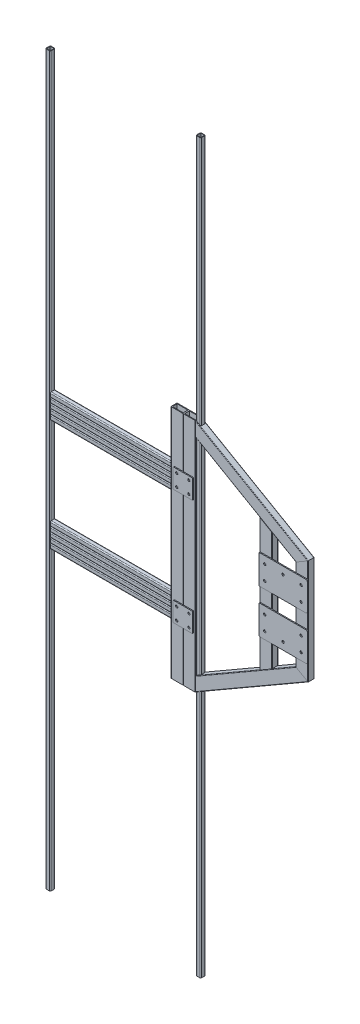
SolidWorks part; units mm, degrees
ref_plane "Front Plane" through (0, 0, 0) normal (0, 0, 1) x (1, 0, 0)
ref_plane "Top Plane" through (0, 0, 0) normal (0, 1, 0) x (1, 0, 0)
ref_plane "Right Plane" through (0, 0, 0) normal (1, 0, 0) x (0, 0, -1)
sketch "Sketch1" plane through (0, 0, 0) normal (0, 0, 1) x (1, 0, 0)
  line L0 (0, 0) -> (600, 0)
  line L1 (0, 20) -> (600, 20)
  line L2 (0, 40) -> (600, 40)
  line L3 (0, 60) -> (600, 60)
  line L4 (0, 80) -> (600, 80)
  line L5 (0, 460) -> (600, 460)
  line L6 (0, 480) -> (600, 480)
  line L7 (0, 500) -> (600, 500)
  line L8 (0, 520) -> (600, 520)
  line L10 (0, 540) -> (600, 540)
  dimension "D1" = 600
  dimension "D2" = 3
  dimension "D3" = 2
  dimension "D4" = 2
  dimension "D5" = 2
sketch "Sketch12" plane through (0, 0, 0) normal (0, 0, 1) x (1, 0, 0)
  line L0 (-10, -1232.2841) -> (-10, 1767.7159)
  line L1 (610, -1232.2841) -> (610, 1767.7159)
  line L2 (79.8284, -832.2841) -> (398.8284, -832.2841) construction
  dimension "D1" = 3000
  dimension "D2" = 400
  dimension "D3" = 400
  dimension "D4" = 3000
  dimension "D5" = 10
  dimension "D6" = 10
other "Tube (square) 20 X 20 X 2.0(13)"
ref_plane "Plane4" through (-10, -1232.2841, 0) normal (0, 1, 0) x (-1, 0, 0)
sketch "Sketch15" plane through (-10, -1232.2841, 0) normal (0, 1, 0) x (-1, 0, 0)
  line L0 (-6, -8) -> (6, -8)
  line L1 (-8, -6) -> (-8, 6)
  line L2 (6, 8) -> (-6, 8)
  line L3 (8, 6) -> (8, -6)
  line L4 (-6, -10) -> (6, -10)
  line L5 (-10, -6) -> (-10, 6)
  line L6 (6, 10) -> (-6, 10)
  line L7 (10, 6) -> (10, -6)
  line L8 (-10, 0) -> (-8, 0) construction
  line L9 (-8, 0) -> (8, 0) construction
  line L10 (8, 0) -> (10, 0) construction
  line L12 (0, 10) -> (0, 8) construction
  line L13 (0, 8) -> (0, -8) construction
  line L14 (0, -8) -> (0, -10) construction
  arc A0 (10, 6) -> (6, 10) centre (6, 6) ccw
  arc A1 (6, -10) -> (10, -6) centre (6, -6) ccw
  arc A2 (-10, -6) -> (-6, -10) centre (-6, -6) ccw
  arc A3 (-6, 10) -> (-10, 6) centre (-6, 6) ccw
  arc A4 (-6, 8) -> (-8, 6) centre (-6, 6) ccw
  arc A5 (8, 6) -> (6, 8) centre (6, 6) ccw
  arc A6 (6, -8) -> (8, -6) centre (6, -6) ccw
  arc A7 (-8, -6) -> (-6, -8) centre (-6, -6) ccw
  point P2 (-10, 10)
  point P33 (-10, -10)
  point P34 (10, -10)
  point P36 (10, 10)
  point P37 (0, 0)
  dimension "D1" = 4
  dimension "Thickness" = 2
  dimension "V_leg" = 20
  dimension "H_leg" = 20
other "Tube (square) 20 X 20 X 2.0(14)"
ref_plane "Plane5" through (0, 0, 0) normal (1, 0, 0) x (0, 1, 0)
sketch "Sketch16" plane through (0, 0, 0) normal (1, 0, 0) x (0, 1, 0)
  line L0 (-6, -8) -> (6, -8)
  line L1 (-8, -6) -> (-8, 6)
  line L2 (6, 8) -> (-6, 8)
  line L3 (8, 6) -> (8, -6)
  line L4 (-6, -10) -> (6, -10)
  line L5 (-10, -6) -> (-10, 6)
  line L6 (6, 10) -> (-6, 10)
  line L7 (10, 6) -> (10, -6)
  line L8 (-10, 0) -> (-8, 0) construction
  line L9 (-8, 0) -> (8, 0) construction
  line L10 (8, 0) -> (10, 0) construction
  line L12 (0, 10) -> (0, 8) construction
  line L13 (0, 8) -> (0, -8) construction
  line L14 (0, -8) -> (0, -10) construction
  arc A0 (10, 6) -> (6, 10) centre (6, 6) ccw
  arc A1 (6, -10) -> (10, -6) centre (6, -6) ccw
  arc A2 (-10, -6) -> (-6, -10) centre (-6, -6) ccw
  arc A3 (-6, 10) -> (-10, 6) centre (-6, 6) ccw
  arc A4 (-6, 8) -> (-8, 6) centre (-6, 6) ccw
  arc A5 (8, 6) -> (6, 8) centre (6, 6) ccw
  arc A6 (6, -8) -> (8, -6) centre (6, -6) ccw
  arc A7 (-8, -6) -> (-6, -8) centre (-6, -6) ccw
  point P2 (-10, 10)
  point P33 (-10, -10)
  point P34 (10, -10)
  point P36 (10, 10)
  point P37 (0, 0)
  dimension "D1" = 4
  dimension "Thickness" = 2
  dimension "V_leg" = 20
  dimension "H_leg" = 20
sketch "Sketch17" plane through (0, 0, 0) normal (0, 0, 1) x (1, 0, 0)
  line L0 (576.0753, -203.8885) -> (1040, 63.9586)
  line L1 (610, -1232.2841) -> (610, 1767.7159) construction
  line L3 (1040, 467.4374) -> (576.0753, 735.2844)
  line L5 (1040, 63.9586) -> (1040, 467.4374)
  line L8 (620, 1767.7159) -> (620, -1232.2841) construction
  line L9 (891.0801, -22.0204) -> (891.0801, 553.4163)
  line L10 (576.0753, -219.302) -> (576.0753, 750.698)
  line L11 (525.2753, -219.302) -> (525.2753, 750.698)
  dimension "D1" = 60
  dimension "D2" = 60
  dimension "D3" = 50.8
  dimension "D5" = 420
  dimension "D6" = 970
other "Tube (rectangular) RECT(15)"
ref_plane "Plane6" through (1040, 63.9586, 0) normal (0, 1, 0) x (-1, 0, 0)
sketch "Sketch112" plane through (1040, 63.9586, 0) normal (0, 1, 0) x (-1, 0, 0)
  line L0 (22.4, 9.7) -> (-22.4, 9.7)
  line L1 (23.4, 12.7) -> (-23.4, 12.7)
  line L2 (25.4, 10.7) -> (25.4, -10.7)
  line L3 (23.4, -12.7) -> (-23.4, -12.7)
  line L4 (-25.4, 10.7) -> (-25.4, -10.7)
  line L5 (25.4, 12.7) -> (-25.4, -12.7) construction
  line L6 (25.4, -12.7) -> (-25.4, 12.7) construction
  line L7 (-22.4, 9.7) -> (-22.4, -9.7)
  line L8 (22.4, -9.7) -> (-22.4, -9.7)
  line L9 (22.4, 9.7) -> (22.4, -9.7)
  line L10 (25.4, 12.7) -> (-25.4, 12.7) construction
  line L11 (25.4, 12.7) -> (25.4, -12.7) construction
  line L12 (25.4, -12.7) -> (-25.4, -12.7) construction
  line L13 (-25.4, 12.7) -> (-25.4, -12.7) construction
  arc A0 (23.4, 12.7) -> (25.4, 10.7) centre (23.4, 10.7) cw
  arc A1 (25.4, -10.7) -> (23.4, -12.7) centre (23.4, -10.7) cw
  arc A2 (-23.4, -12.7) -> (-25.4, -10.7) centre (-23.4, -10.7) cw
  arc A3 (-25.4, 10.7) -> (-23.4, 12.7) centre (-23.4, 10.7) cw
  point P0 (0, 0)
  point P22 (0, 0)
  dimension "D4" = 2
  dimension "D1" = 50.8
  dimension "D2" = 25.4
  dimension "D3" = 3
other "Tube (rectangular) RECT(16)"
ref_plane "Plane7" through (1040, 467.4374, 0) normal (-0.866, 0.5, 0) x (-0.5, -0.866, 0)
sketch "Sketch113" plane through (1040, 467.4374, 0) normal (-0.866, 0.5, 0) x (-0.5, -0.866, 0)
  line L0 (22.4, 9.7) -> (-22.4, 9.7)
  line L1 (23.4, 12.7) -> (-23.4, 12.7)
  line L2 (25.4, 10.7) -> (25.4, -10.7)
  line L3 (23.4, -12.7) -> (-23.4, -12.7)
  line L4 (-25.4, 10.7) -> (-25.4, -10.7)
  line L5 (25.4, 12.7) -> (-25.4, -12.7) construction
  line L6 (25.4, -12.7) -> (-25.4, 12.7) construction
  line L7 (-22.4, 9.7) -> (-22.4, -9.7)
  line L8 (22.4, -9.7) -> (-22.4, -9.7)
  line L9 (22.4, 9.7) -> (22.4, -9.7)
  line L10 (25.4, 12.7) -> (-25.4, 12.7) construction
  line L11 (25.4, 12.7) -> (25.4, -12.7) construction
  line L12 (25.4, -12.7) -> (-25.4, -12.7) construction
  line L13 (-25.4, 12.7) -> (-25.4, -12.7) construction
  arc A0 (23.4, 12.7) -> (25.4, 10.7) centre (23.4, 10.7) cw
  arc A1 (25.4, -10.7) -> (23.4, -12.7) centre (23.4, -10.7) cw
  arc A2 (-23.4, -12.7) -> (-25.4, -10.7) centre (-23.4, -10.7) cw
  arc A3 (-25.4, 10.7) -> (-23.4, 12.7) centre (-23.4, 10.7) cw
  point P0 (0, 0)
  point P22 (0, 0)
  dimension "D4" = 2
  dimension "D1" = 50.8
  dimension "D2" = 25.4
  dimension "D3" = 3
other "Tube (rectangular) RECT(17)"
ref_plane "Plane8" through (576.0753, -203.8885, 0) normal (0.866, 0.5, 0) x (-0.5, 0.866, 0)
sketch "Sketch114" plane through (576.0753, -203.8885, 0) normal (0.866, 0.5, 0) x (-0.5, 0.866, 0)
  line L0 (22.4, 9.7) -> (-22.4, 9.7)
  line L1 (23.4, 12.7) -> (-23.4, 12.7)
  line L2 (25.4, 10.7) -> (25.4, -10.7)
  line L3 (23.4, -12.7) -> (-23.4, -12.7)
  line L4 (-25.4, 10.7) -> (-25.4, -10.7)
  line L5 (25.4, 12.7) -> (-25.4, -12.7) construction
  line L6 (25.4, -12.7) -> (-25.4, 12.7) construction
  line L7 (-22.4, 9.7) -> (-22.4, -9.7)
  line L8 (22.4, -9.7) -> (-22.4, -9.7)
  line L9 (22.4, 9.7) -> (22.4, -9.7)
  line L10 (25.4, 12.7) -> (-25.4, 12.7) construction
  line L11 (25.4, 12.7) -> (25.4, -12.7) construction
  line L12 (25.4, -12.7) -> (-25.4, -12.7) construction
  line L13 (-25.4, 12.7) -> (-25.4, -12.7) construction
  arc A0 (23.4, 12.7) -> (25.4, 10.7) centre (23.4, 10.7) cw
  arc A1 (25.4, -10.7) -> (23.4, -12.7) centre (23.4, -10.7) cw
  arc A2 (-23.4, -12.7) -> (-25.4, -10.7) centre (-23.4, -10.7) cw
  arc A3 (-25.4, 10.7) -> (-23.4, 12.7) centre (-23.4, 10.7) cw
  point P0 (0, 0)
  point P22 (0, 0)
  dimension "D4" = 2
  dimension "D1" = 50.8
  dimension "D2" = 25.4
  dimension "D3" = 3
other "Trim/Extend1"
other "Trim/Extend2"
other "Trim/Extend5"
other "Trim/Extend6"
other "Trim/Extend9"
sketch "Sketch116" plane through (0, 0, 12.7) normal (0, 0, 1) x (1, 0, 0)
  line L0 (1066.0801, 410.698) -> (1066.0801, 120.698) construction
  line L1 (866.0801, 115.698) -> (1066.0801, 115.698)
  line L2 (866.0801, 115.698) -> (866.0801, 235.698)
  line L3 (866.0801, 235.698) -> (1066.0801, 235.698)
  line L4 (513.344, 65.9676) -> (513.344, -10.0324)
  line L5 (515.344, -12.0324) -> (591.344, -12.0324)
  line L6 (593.344, -10.0324) -> (593.344, 65.9676)
  line L7 (591.344, 67.9676) -> (515.344, 67.9676)
  line L8 (513.344, 65.9676) -> (513.344, -10.0324)
  line L9 (515.344, -12.0324) -> (591.344, -12.0324)
  line L10 (593.344, -10.0324) -> (593.344, 65.9676)
  line L11 (591.344, 67.9676) -> (515.344, 67.9676)
  line L12 (593.344, 465.9551) -> (593.344, 541.9551)
  line L13 (591.344, 543.9551) -> (515.344, 543.9551)
  line L14 (513.344, 541.9551) -> (513.344, 465.9551)
  line L15 (515.344, 463.9551) -> (591.344, 463.9551)
  line L16 (593.344, 465.9551) -> (593.344, 541.9551)
  line L17 (591.344, 543.9551) -> (515.344, 543.9551)
  line L18 (513.344, 541.9551) -> (513.344, 465.9551)
  line L19 (515.344, 463.9551) -> (591.344, 463.9551)
  line L20 (1066.0801, 115.698) -> (1066.0801, 235.698)
  line L21 (871.0801, 115.698) -> (1061.0801, 115.698) construction
  line L23 (866.0801, 415.698) -> (1066.0801, 415.698)
  line L24 (866.0801, 415.698) -> (866.0801, 295.698)
  line L25 (866.0801, 295.698) -> (1066.0801, 295.698)
  line L26 (1066.0801, 295.698) -> (1066.0801, 415.698)
  circle A0 centre (528.344, 2.9676) radius 5 construction
  circle A1 centre (578.344, 2.9676) radius 5 construction
  circle A2 centre (578.344, 52.9676) radius 5 construction
  circle A3 centre (528.344, 52.9676) radius 5 construction
  arc A4 (513.344, -10.0324) -> (515.344, -12.0324) centre (515.344, -10.0324) ccw
  arc A5 (591.344, -12.0324) -> (593.344, -10.0324) centre (591.344, -10.0324) ccw
  arc A6 (593.344, 65.9676) -> (591.344, 67.9676) centre (591.344, 65.9676) ccw
  arc A7 (515.344, 67.9676) -> (513.344, 65.9676) centre (515.344, 65.9676) ccw
  arc A8 (513.344, -10.0324) -> (515.344, -12.0324) centre (515.344, -10.0324) ccw
  arc A9 (591.344, -12.0324) -> (593.344, -10.0324) centre (591.344, -10.0324) ccw
  arc A10 (593.344, 65.9676) -> (591.344, 67.9676) centre (591.344, 65.9676) ccw
  arc A11 (515.344, 67.9676) -> (513.344, 65.9676) centre (515.344, 65.9676) ccw
  arc A12 (593.344, 541.9551) -> (591.344, 543.9551) centre (591.344, 541.9551) ccw
  arc A13 (515.344, 543.9551) -> (513.344, 541.9551) centre (515.344, 541.9551) ccw
  arc A14 (513.344, 465.9551) -> (515.344, 463.9551) centre (515.344, 465.9551) ccw
  arc A15 (591.344, 463.9551) -> (593.344, 465.9551) centre (591.344, 465.9551) ccw
  arc A16 (593.344, 541.9551) -> (591.344, 543.9551) centre (591.344, 541.9551) ccw
  arc A17 (515.344, 543.9551) -> (513.344, 541.9551) centre (515.344, 541.9551) ccw
  arc A18 (513.344, 465.9551) -> (515.344, 463.9551) centre (515.344, 465.9551) ccw
  arc A19 (591.344, 463.9551) -> (593.344, 465.9551) centre (591.344, 465.9551) ccw
  circle A20 centre (528.344, 478.9551) radius 5 construction
  circle A21 centre (578.344, 478.9551) radius 5 construction
  circle A22 centre (528.344, 528.9551) radius 5 construction
  circle A23 centre (578.344, 528.9551) radius 5 construction
  circle A24 centre (528.344, 2.9676) radius 5
  circle A25 centre (578.344, 2.9676) radius 5
  circle A26 centre (578.344, 52.9676) radius 5
  circle A27 centre (528.344, 52.9676) radius 5
  circle A28 centre (528.344, 478.9551) radius 5
  circle A29 centre (578.344, 478.9551) radius 5
  circle A30 centre (528.344, 528.9551) radius 5
  circle A31 centre (578.344, 528.9551) radius 5
  circle A32 centre (891.0801, 205.698) radius 5 construction
  circle A33 centre (1041.0801, 205.698) radius 5 construction
  circle A34 centre (891.0801, 145.698) radius 5 construction
  circle A35 centre (966.0801, 145.698) radius 5 construction
  circle A36 centre (1041.0801, 145.698) radius 5 construction
  circle A37 centre (891.0801, 325.698) radius 5 construction
  circle A38 centre (891.0801, 385.698) radius 5 construction
  circle A39 centre (966.0801, 385.698) radius 5 construction
  circle A40 centre (1041.0801, 325.698) radius 5 construction
  circle A41 centre (1041.0801, 385.698) radius 5 construction
  circle A42 centre (891.0801, 205.698) radius 5
  circle A43 centre (1041.0801, 205.698) radius 5
  circle A44 centre (891.0801, 145.698) radius 5
  circle A45 centre (966.0801, 145.698) radius 5
  circle A46 centre (1041.0801, 145.698) radius 5
  circle A47 centre (891.0801, 325.698) radius 5
  circle A48 centre (891.0801, 385.698) radius 5
  circle A49 centre (966.0801, 385.698) radius 5
  circle A50 centre (1041.0801, 325.698) radius 5
  circle A51 centre (1041.0801, 385.698) radius 5
  dimension "D3" = 30
  dimension "D4" = 0
  dimension "D5" = 30
  dimension "D6" = 120
  dimension "D1" = 0
  dimension "D2" = 0
extrude "Boss-Extrude1" add sketch "Sketch116" along normal blind 4 separate body
fillet "Fillet1" radius 5 4 edges at (1066.0801, 235.698, 14.7) (866.0801, 235.698, 14.7) (1066.0801, 115.698, 14.7) (866.0801, 115.698, 14.7)
fillet "Fillet2" radius 5 4 edges at (866.0801, 295.698, 14.7) (866.0801, 415.698, 14.7) (1066.0801, 415.698, 14.7) (1066.0801, 295.698, 14.7)
